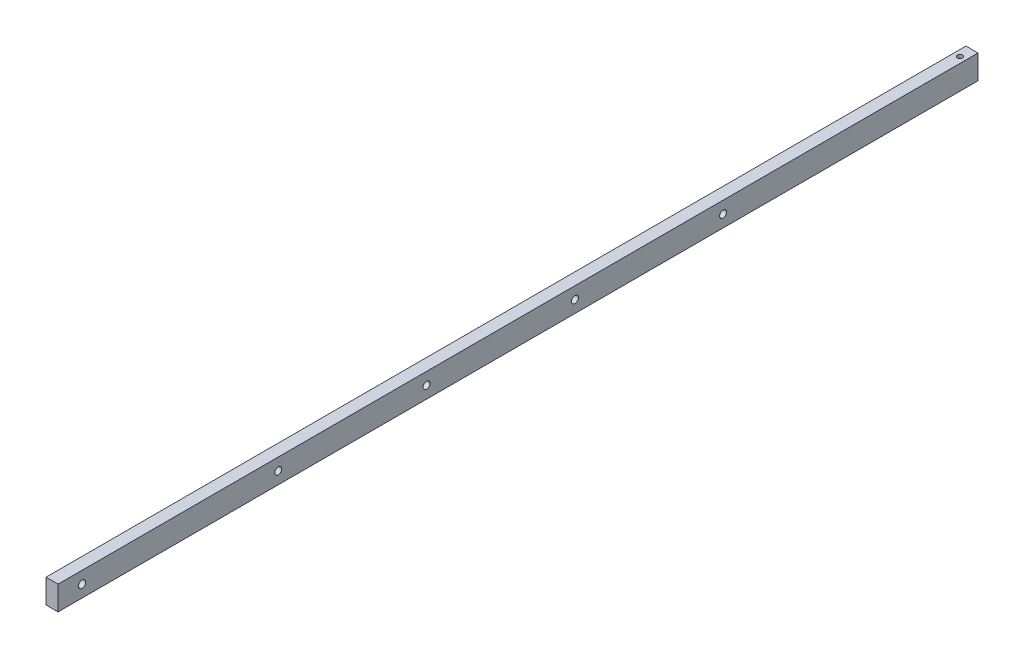
SolidWorks part; units mm, degrees
material "6061 Alloy"
ref_plane "Front Plane" through (0, 0, 0) normal (0, 0, 1) x (1, 0, 0)
ref_plane "Top Plane" through (0, 0, 0) normal (0, 1, 0) x (1, 0, 0)
ref_plane "Right Plane" through (0, 0, 0) normal (1, 0, 0) x (0, 0, -1)
sketch "Sketch1" plane through (0, 0, 0) normal (0, 0, 1) x (1, 0, 0)
  line L1 (0, 0) -> (6.35, 0)
  line L2 (0, 0) -> (0, 12.7)
  line L3 (0, 12.7) -> (6.35, 12.7)
  line L4 (6.35, 0) -> (6.35, 12.7)
  dimension "D1" = 12.7
extrude "Boss-Extrude1" add sketch "Sketch1" along normal blind 485.14
hole_wizard "#6 Clearance Hole1" positions "Sketch5" profile "Sketch4" hole size "#6" standard "ANSI Inch" end condition through all
sketch "Sketch5" plane through (6.35, 0, 0) normal (1, 0, 0) x (0, 0, -1)
  line L0 (-485.14, 0) -> (-485.14, 12.7) construction
  line L1 (-485.14, 12.7) -> (0, 12.7) construction
  point P0 (-472.44, 6.35)
  dimension "D1" = 12.7
  dimension "D2" = 6.35
sketch "Sketch4" plane through (6.35, 6.35, 472.44) normal (0, 1, 0) x (0, 0, -1)
  line L0 (0, 0) -> (0, 6.35)
  line L1 (0, 6.35) -> (1.8986, 6.35)
  line L2 (1.8986, 6.35) -> (1.8986, 0)
  line L5 (1.8986, 0) -> (0, 0)
  line L11 (0, -6.35) -> (0, 107.95) construction
  dimension "Thru Hole Dia." = 3.7973
  dimension "Thru Hole Depth" = 6.35
hole_wizard "Tap Drill for #6-32 Tap1" positions "Sketch7" profile "Sketch6" hole size "#6-32" standard "ANSI Inch" end condition through all
sketch "Sketch7" plane through (0, 12.7, 0) normal (0, 1, 0) x (1, 0, 0)
  line L0 (6.35, 0) -> (0, 0) construction
  line L1 (0, -485.14) -> (0, 0) construction
  point P0 (3.175, -6.35)
  dimension "D1" = 6.35
  dimension "D2" = 3.175
sketch "Sketch6" plane through (3.175, 12.7, 6.35) normal (1, 0, 0) x (0, 0, 1)
  line L0 (0, 0) -> (0, 12.7)
  line L1 (0, 12.7) -> (1.3525, 12.7)
  line L2 (1.3525, 12.7) -> (1.3525, 0)
  line L5 (1.3525, 0) -> (0, 0)
  line L11 (0, -6.35) -> (0, 107.95) construction
  dimension "Thru Hole Dia." = 2.7051
  dimension "Thru Hole Depth" = 12.7
hole_wizard "#6 Clearance Hole2" positions "Sketch8" profile "Sketch9" hole size "#6" standard "ANSI Inch" end condition through all
sketch "Sketch8" plane through (0, 1342.1184, -1739.8094) normal (-1, 0, 0) x (0, 0, -1)
  line L1 (-2224.9494, 1335.7684) -> (-1739.8094, 1335.7684) construction
  line L5 (-2126.3688, 1342.1184) -> (-2126.3688, 1329.4184) construction
  line L9 (-2126.3688, 1329.4184) -> (-2091.3168, 1342.1184) construction
  line L11 (-2091.3168, 1342.1184) -> (-2091.3168, 1329.4184) construction
  line L14 (-2048.1368, 1345.0634) -> (-2048.1368, 1329.4184) construction
  line L15 (-2048.1368, 1329.4184) -> (-2013.0848, 1342.1184) construction
  line L17 (-2013.0848, 1342.1184) -> (-2013.0848, 1329.4184) construction
  line L18 (-2013.0848, 1329.4184) -> (-1969.9048, 1342.1184) construction
  line L20 (-1969.9048, 1342.1184) -> (-1969.9048, 1329.4184) construction
  line L21 (-1969.9048, 1329.4184) -> (-1934.8528, 1342.1184) construction
  line L22 (-1934.8528, 1342.1184) -> (-1934.8528, 1329.4184) construction
  line L23 (-1934.8528, 1329.4184) -> (-1891.6728, 1342.1184) construction
  line L25 (-1891.6728, 1342.1184) -> (-1856.8072, 1329.4184) construction
  line L27 (-1856.8072, 1329.4184) -> (-1813.6272, 1342.1184) construction
  line L30 (-2091.3168, 1329.4184) -> (-2048.1368, 1342.1184) construction
  point P72 (-2108.8428, 1335.7684)
  point P78 (-1952.3788, 1335.7684)
  point P86 (-2030.6108, 1335.7684)
  point P88 (-1874.24, 1335.7684)
sketch "Sketch9" plane through (0, 6.35, 369.0334) normal (0, 1, 0) x (0, 0, 1)
  line L0 (0, 0) -> (0, 6.35)
  line L1 (0, 6.35) -> (1.8288, 6.35)
  line L2 (1.8288, 6.35) -> (1.8288, 0)
  line L3 (1.8288, 0) -> (0, 0)
  line L4 (0, -6.35) -> (0, 107.95) construction
  dimension "Thru Hole Dia." = 3.6576
  dimension "Thru Hole Depth" = 6.35
